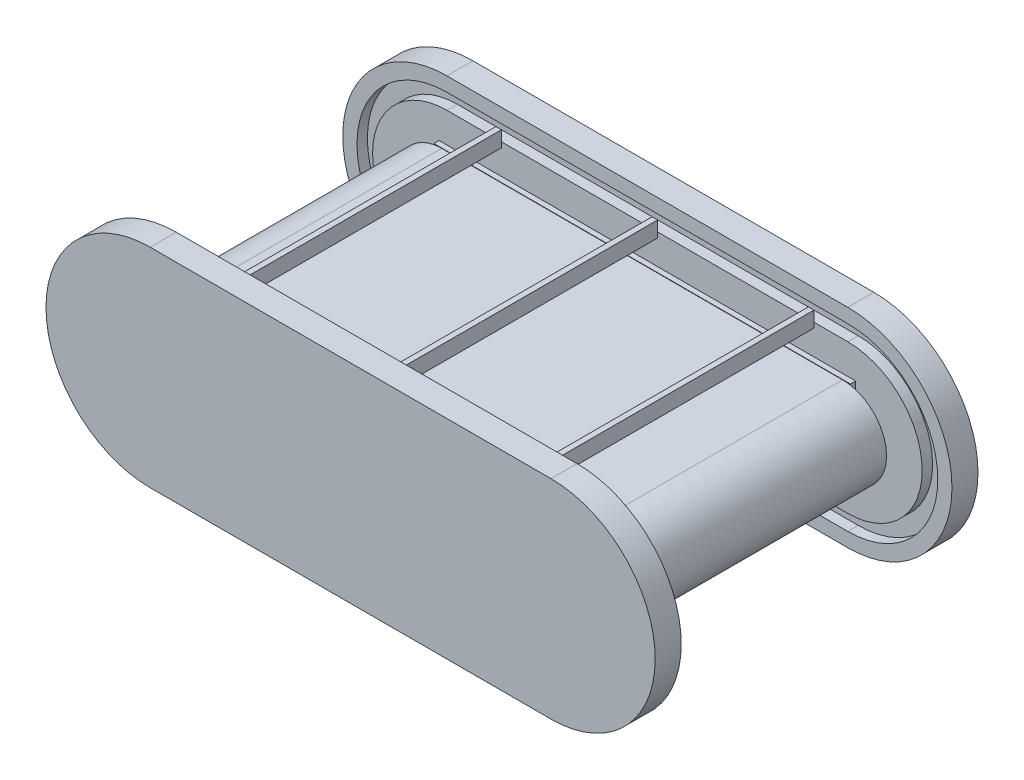
SolidWorks part; units mm, degrees
ref_plane "Front Plane" through (0, 0, 0) normal (0, 0, 1) x (1, 0, 0)
ref_plane "Top Plane" through (0, 0, 0) normal (0, 1, 0) x (1, 0, 0)
ref_plane "Right Plane" through (0, 0, 0) normal (1, 0, 0) x (0, 0, -1)
sketch "Sketch3" plane through (0, 0, 0) normal (0, 0, 1) x (1, 0, 0)
  line L0 (-260, 85) -> (540, 85)
  line L1 (-230, 75) -> (510, 75)
  line L3 (-230, -75) -> (510, -75)
  line L6 (-260, -85) -> (540, -85)
  line L8 (-250, -75) -> (530, -75) construction
  line L9 (530, 75) -> (530, -75) construction
  line L10 (-250, 75) -> (530, 75) construction
  line L14 (510, 75) -> (510, -75)
  line L15 (540, 85) -> (540, -85)
  line L19 (-230, 75) -> (-230, -75)
  line L20 (-250, 75) -> (-250, -75) construction
  line L21 (540, 85) -> (540, -85) construction
  line L22 (-260, 85) -> (-260, -85)
  line L23 (-260, 85) -> (-260, -85) construction
  point P0 (0, 0)
  dimension "D1" = 170
  dimension "D2" = 150
  dimension "D4" = 800
  dimension "D5" = 740
extrude "Boss-Extrude1" add sketch "Sketch3" along normal blind 10
sketch "Sketch4" plane through (0, 0, 10) normal (0, 0, 1) x (1, 0, 0)
  line L0 (-230, 0) -> (-260, 0) construction
  line L1 (-230, 75) -> (-230, -75) construction
  line L2 (-260, 85) -> (-260, -85) construction
  line L7 (-245, 84.2894) -> (525, 84.2894)
  line L8 (-245, -84.2894) -> (525, -84.2894)
  line L9 (-245, 74.2894) -> (525, 74.2894)
  line L10 (-245, -74.2894) -> (525, -74.2894)
  arc A1 (525, -84.2894) -> (525, 84.2894) centre (525, 0) ccw
  arc A2 (-245, 84.2894) -> (-245, -84.2894) centre (-245, 0) ccw
  arc A3 (525, -74.2894) -> (525, 74.2894) centre (525, 0) ccw
  arc A4 (-245, 74.2894) -> (-245, -74.2894) centre (-245, 0) ccw
  dimension "D1" = 10
extrude "Boss-Extrude2" add sketch "Sketch4" along normal blind 500
sketch "Sketch5" plane through (0, 0, 510) normal (0, 0, 1) x (1, 0, 0)
  line L1 (-260, 85) -> (540, 85)
  line L2 (-260, 85) -> (-260, -85)
  line L3 (-260, -85) -> (540, -85)
  line L4 (540, 85) -> (540, -85)
  line L5 (-230, 74.2894) -> (510, 74.2894)
  line L6 (-230, 74.2894) -> (-230, -74.2894)
  line L7 (-230, -74.2894) -> (510, -74.2894)
  line L8 (510, 74.2894) -> (510, -74.2894)
extrude "Boss-Extrude3" add sketch "Sketch5" along normal blind 10
sketch "Sketch6" plane through (0, 0, 520) normal (0, 0, 1) x (1, 0, 0)
  circle A0 centre (-245, 0) radius 10
  circle A1 centre (525, 0) radius 10
  dimension "D1" = 20
  dimension "D2" = 20
sketch "Sketch7" plane through (0, 0, 10) normal (0, 0, 1) x (1, 0, 0)
  circle A0 centre (-245, 0) radius 74.2894
  circle A1 centre (525, 0) radius 74.2894
extrude "Boss-Extrude6" add sketch "Sketch7" along normal up to surface (500 mm away) up to face at (525.013, 0, 510)
extrude "Cut-Extrude1" cut sketch "Sketch6" against normal through all
sketch "Sketch8" plane through (0, 0, 520) normal (0, 0, 1) x (1, 0, 0)
  line L0 (-245, 200) -> (525, 200)
  line L1 (-245, -200) -> (525, -200)
  arc A0 (-245, 200) -> (-245, -200) centre (-245, 0) ccw
  arc A1 (525, -200) -> (525, 200) centre (525, 0) ccw
  dimension "D1" = 400
extrude "Boss-Extrude8" add sketch "Sketch8" along normal blind 50
sketch "Sketch9" plane through (0, 0, 520) normal (0, 0, -1) x (-1, 0, 0)
  line L0 (-525, 172.7437) -> (245, 172.7437)
  line L1 (-525, -172.7437) -> (245, -172.7437)
  line L2 (-525, -142.7437) -> (245, -142.7437)
  line L3 (-525, 142.7437) -> (245, 142.7437)
  arc A0 (245, -172.7437) -> (245, 172.7437) centre (245, 0) ccw
  arc A1 (245, -142.7437) -> (245, 142.7437) centre (245, 0) ccw
  arc A2 (-525, 172.7437) -> (-525, -172.7437) centre (-525, 0) ccw
  arc A3 (-525, 142.7437) -> (-525, -142.7437) centre (-525, 0) ccw
  circle A4 centre (245, 0) radius 172.7437 construction
  circle A5 centre (245, 0) radius 142.7437 construction
  dimension "D1" = 30
extrude "Cut-Extrude2" cut sketch "Sketch9" against normal blind 20
sketch "Sketch10" plane through (0, 0, 540) normal (0, 0, -1) x (-1, 0, 0)
  line L0 (245, 172.7437) -> (-525, 172.7437) construction
  line L1 (130.2133, 172.7437) -> (140.8273, 172.7437)
  line L2 (130.2133, 172.7437) -> (130.2133, 142.7437)
  line L3 (130.2133, 142.7437) -> (140.8273, 142.7437)
  line L4 (140.8273, 172.7437) -> (140.8273, 142.7437)
  line L5 (245, 142.7437) -> (-525, 142.7437) construction
  line L6 (-169.7867, 172.7437) -> (-159.1727, 172.7437)
  line L7 (-169.7867, 172.7437) -> (-169.7867, 142.7437)
  line L8 (-169.7867, 142.7437) -> (-159.1727, 142.7437)
  line L9 (-159.1727, 172.7437) -> (-159.1727, 142.7437)
  line L10 (-469.7867, 172.7437) -> (-459.1727, 172.7437)
  line L11 (-469.7867, 172.7437) -> (-469.7867, 142.7437)
  line L12 (-469.7867, 142.7437) -> (-459.1727, 142.7437)
  line L13 (-459.1727, 172.7437) -> (-459.1727, 142.7437)
  dimension "D1" = 3
extrude "Boss-Extrude9" add sketch "Sketch10" along normal blind 530
ref_plane "Plane1" through (0, 0, 260) normal (0, 0, -1) x (-1, 0, 0)
mirror "Mirror1" about plane through (0, 0, 260) normal (0, 0, -1) of "Cut-Extrude2", "Boss-Extrude8"
